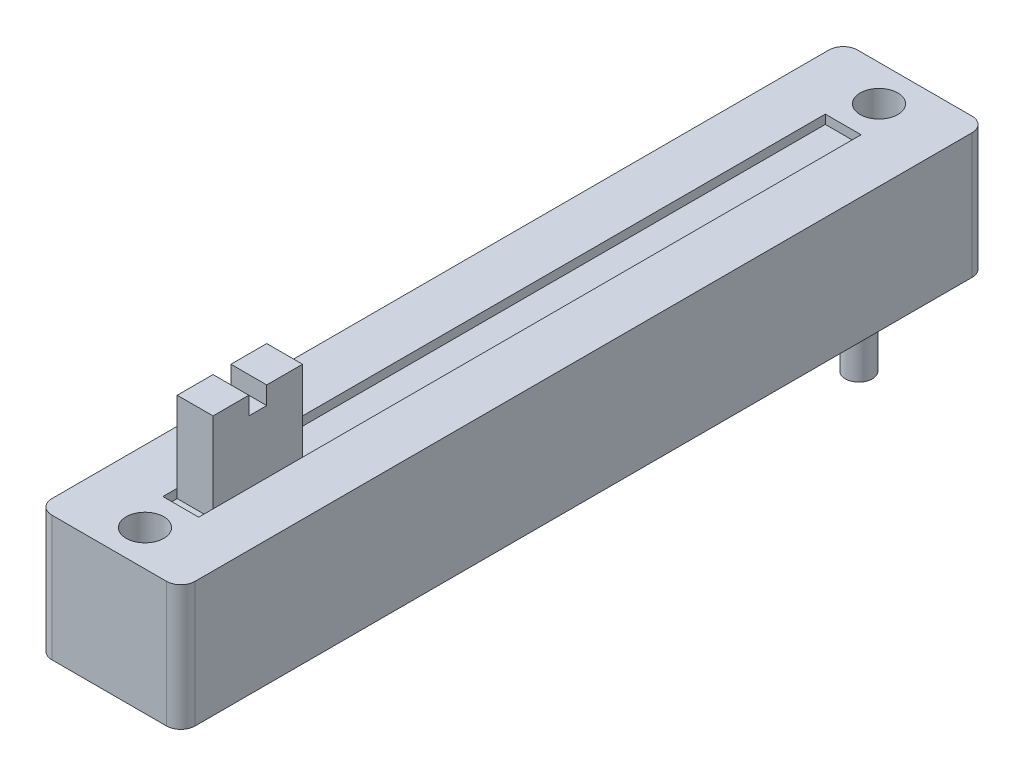
SolidWorks part; units mm, degrees
ref_plane "Płaszczyzna przednia" through (0, 0, 0) normal (0, 0, 1) x (1, 0, 0)
ref_plane "Płaszczyzna górna" through (0, 0, 0) normal (0, 1, 0) x (1, 0, 0)
ref_plane "Płaszczyzna prawa" through (0, 0, 0) normal (1, 0, 0) x (0, 0, -1)
sketch "Szkic1" plane through (0, 0, 0) normal (0, 1, 0) x (1, 0, 0)
  line L1 (0, 0) -> (8, 0)
  line L2 (0, 0) -> (0, 45)
  line L3 (0, 45) -> (8, 45)
  line L4 (8, 0) -> (8, 45)
  dimension "D1" = 45
  dimension "D2" = 8
extrude "Dodanie-wyciągnięcie1" add sketch "Szkic1" along normal blind 7
sketch "Szkic2" plane through (0, 7, 0) normal (0, 1, 0) x (1, 0, 0)
  line L0 (8, 45) -> (0, 45) construction
  line L2 (0, 0) -> (8, 0) construction
  circle A0 centre (4, 2) radius 1.05
  circle A1 centre (4, 43) radius 1.05
  dimension "D2" = 2.1
  dimension "D3" = 2.1
  dimension "D4" = 2
  dimension "D1" = 2
extrude "Wytnij-wyciągnięcie1" cut sketch "Szkic2" against normal blind 7
sketch "Szkic3" plane through (0, 7, 0) normal (0, 1, 0) x (1, 0, 0)
  line L1 (3, 4) -> (5, 4)
  line L2 (3, 4) -> (3, 41)
  line L3 (3, 41) -> (5, 41)
  line L4 (5, 4) -> (5, 41)
  line L5 (0, 0) -> (8, 0) construction
  line L6 (8, 0) -> (8, 45) construction
  point P6 (4, 0)
  point P7 (4, 4)
  point P8 (8, 22.5)
  point P11 (5, 22.5)
  dimension "D1" = 37
  dimension "D2" = 2
extrude "Wytnij-wyciągnięcie2" cut sketch "Szkic3" against normal blind 0.5
sketch "Szkic4" plane through (0, 6.5, 0) normal (0, 1, 0) x (1, 0, 0)
  line L0 (5, 4) -> (5, 41) construction
  line L1 (3, 4.8) -> (5, 4.8)
  line L2 (3, 4.8) -> (3, 9.8)
  line L3 (3, 9.8) -> (5, 9.8)
  line L4 (5, 4.8) -> (5, 9.8)
  line L5 (3, 4) -> (5, 4) construction
  line L7 (3, 41) -> (3, 4) construction
  dimension "D1" = 5
  dimension "D2" = 0.8
extrude "Dodanie-wyciągnięcie4" add sketch "Szkic4" along normal blind 5
sketch "Szkic13" plane through (0, 0, 0) normal (0, -1, 0) x (1, 0, 0)
  line L0 (4, -45) -> (4, 0) construction
  line L1 (8, -45) -> (0, -45) construction
  line L2 (0, 0) -> (8, 0) construction
  line L3 (0, -22.5) -> (8, -22.5) construction
  line L4 (0, -45) -> (0, 0) construction
  line L5 (8, 0) -> (8, -45) construction
  circle A0 centre (2.125, -40) radius 0.75
  circle A1 centre (5.875, -40) radius 0.75
  circle A2 centre (2.125, -5) radius 0.75
  point P18 (5.875, -5)
  point P19 (2.125, -5)
  point P20 (0, 0)
  dimension "D1" = 1.5
  dimension "D2" = 17.5
  dimension "D5" = 1.875
  dimension "D3" = 17.5
  dimension "D4" = 3.75
extrude "Dodanie-wyciągnięcie7" add sketch "Szkic13" along normal blind 3.5
fillet "Zaokrąglenie1" radius 0.8 4 edges at (0, 3.5, 0) (8, 3.5, 0) (8, 3.5, -45) (0, 3.5, -45)
sketch "Szkic14" plane through (0, 11.5, 0) normal (0, 1, 0) x (1, 0, 0)
  line L0 (3, 9.8) -> (3, 4.8) construction
  line L1 (3, 6.8) -> (5, 6.8)
  line L2 (3, 6.8) -> (3, 7.8)
  line L3 (3, 7.8) -> (5, 7.8)
  line L4 (5, 6.8) -> (5, 7.8)
  line L5 (5, 4.8) -> (5, 9.8) construction
  point P8 (5, 7.3)
  point P9 (5, 7.3)
  dimension "D1" = 1
extrude "Wytnij-wyciągnięcie3" cut sketch "Szkic14" against normal blind 1
